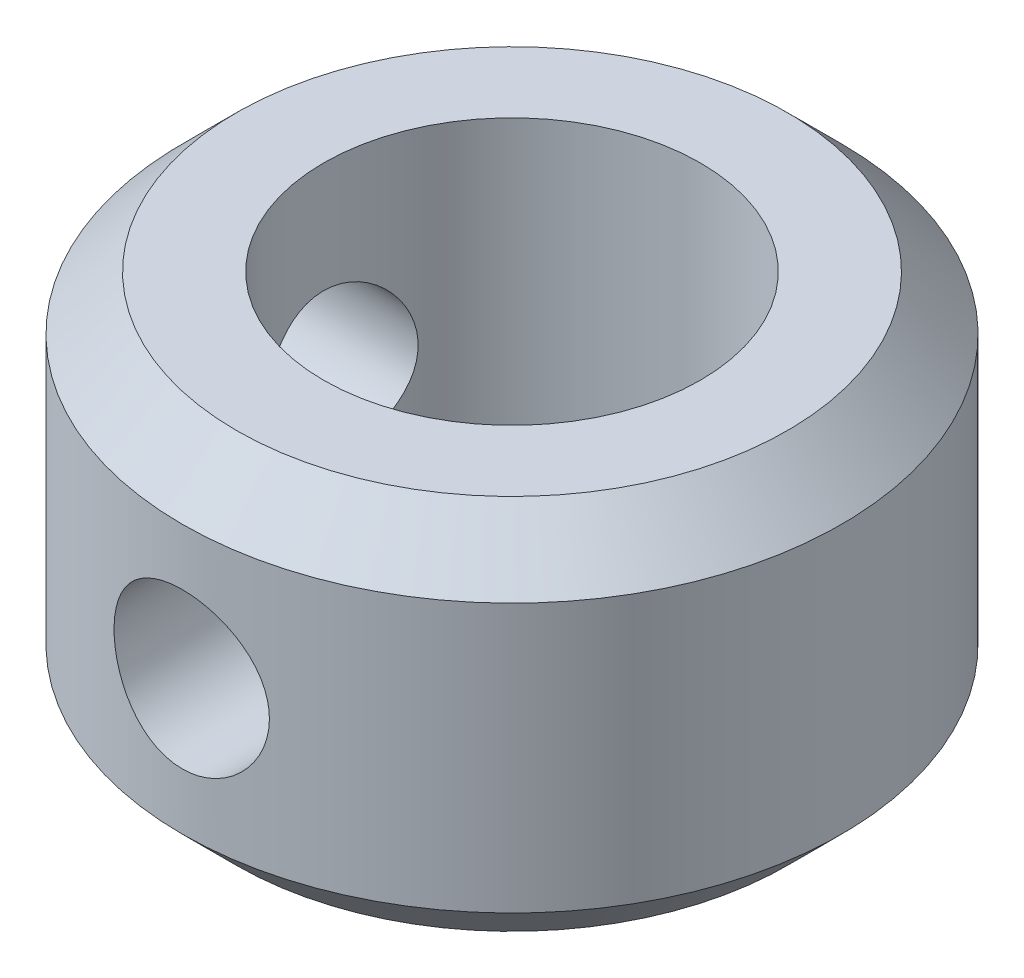
SolidWorks part; units mm, degrees
material "AISI 304"
ref_plane "Front Plane" through (0, 0, 0) normal (0, 0, 1) x (1, 0, 0)
ref_plane "Top Plane" through (0, 0, 0) normal (0, 1, 0) x (1, 0, 0)
ref_plane "Right Plane" through (0, 0, 0) normal (1, 0, 0) x (0, 0, -1)
sketch "Sketch1" plane through (0, 0, 0) normal (0, 1, 0) x (1, 0, 0)
  circle A0 centre (0, 0) radius 7
  circle A1 centre (0, 0) radius 4
  dimension "D1" = 8
  dimension "D2" = 14
extrude "Boss-Extrude1" add sketch "Sketch1" along normal mid plane 8
ref_plane "Plane1" through (0, 0, 7) normal (0, 0, 1) x (1, 0, 0)
hole_wizard "M4x0.7 Tapped Hole1" positions "Sketch2" profile "Sketch3" tap size "M4x0.7" standard "ANSI Metric"
sketch "Sketch2" plane through (0, 0, 7) normal (0, 0, 1) x (1, 0, 0)
  point P0 (0, 0)
sketch "Sketch3" plane through (0, 0, 7) normal (1, 0, 0) x (0, -1, 0)
  line L0 (0, 0) -> (0, 3)
  line L1 (0, 3) -> (1.65, 3)
  line L2 (1.65, 3) -> (1.65, 0)
  line L5 (1.65, 0) -> (0, 0)
  line L11 (0, -6.35) -> (0, 107.95) construction
  dimension "Thru Tap Drill Dia." = 3.3
  dimension "Thru Tap Drill Depth" = 3
cosmetic thread "Hole Thread1"
chamfer "Chamfer1" distance 1.15 angle 45 2 edges at (0, -4, 7) (0, 4, 7)
ref_axis "Axis1" through (0, 4, 0) along (0, -1, 0)
pattern_circular "CirPattern1" count 2 over 90 about axis through (0, 4, 0) along (0, -1, 0) of "M4x0.7 Tapped Hole1"
cosmetic thread "Hole Thread2"
